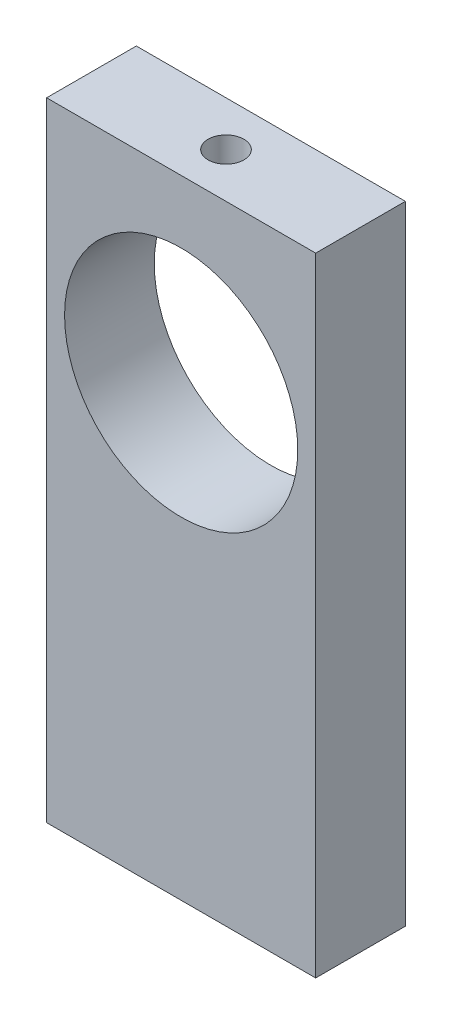
SolidWorks part; units mm, degrees
ref_plane "Front" through (0, 0, 0) normal (0, 0, 1) x (1, 0, 0)
ref_plane "Top" through (0, 0, 0) normal (0, 1, 0) x (1, 0, 0)
ref_plane "Right" through (0, 0, 0) normal (1, 0, 0) x (0, 0, -1)
sketch "Sketch1" plane through (0, 0, 0) normal (0, 0, 1) x (1, 0, 0)
  line L1 (-3.1022, 22.4099) -> (11.8978, 22.4099)
  line L2 (-3.1022, 22.4099) -> (-3.1022, -12.5901)
  line L3 (-3.1022, -12.5901) -> (11.8978, -12.5901)
  line L4 (11.8978, 22.4099) -> (11.8978, -12.5901)
  line L5 (-3.1022, 22.4099) -> (11.8978, -12.5901) construction
  line L6 (-3.1022, -12.5901) -> (11.8978, 22.4099) construction
  point P0 (4.3978, 4.9099)
  dimension "D1" = 35
  dimension "D2" = 15
extrude "Boss-Extrude1" add sketch "Sketch1" along normal blind 5
sketch "Sketch2" plane through (0, 0, 0) normal (0, 0, -1) x (-1, 0, 0)
  line L0 (3.1022, -12.5901) -> (-11.8978, -12.5901) construction
  line L1 (-11.8978, 22.4099) -> (3.1022, 22.4099) construction
  line L2 (-4.3978, -12.5901) -> (-4.3978, 22.4099) construction
  circle A0 centre (-4.3978, 12.4099) radius 6.5
  point P4 (-4.3978, 22.4099)
  dimension "D3" = 13
  dimension "D1" = 25
  dimension "D2" = 0
extrude "Cut-Extrude1" cut sketch "Sketch2" against normal up to surface (5 mm away) up to face at (4.3978, 4.9099, 5)
sketch "Sketch3" plane through (0, 22.4099, 0) normal (0, 1, 0) x (1, 0, 0)
  line L0 (-3.1022, -2.5) -> (11.8978, -2.5) construction
  line L1 (-3.1022, -5) -> (-3.1022, 0) construction
  line L2 (11.8978, -5) -> (11.8978, 0) construction
  line L3 (4.3978, 0) -> (4.3978, -5) construction
  line L4 (11.8978, 0) -> (-3.1022, 0) construction
  line L5 (11.8978, -5) -> (-3.1022, -5) construction
  circle A0 centre (4.3978, -2.5) radius 1
  dimension "D1" = 2
extrude "Cut-Extrude2" cut sketch "Sketch3" against normal up to next
